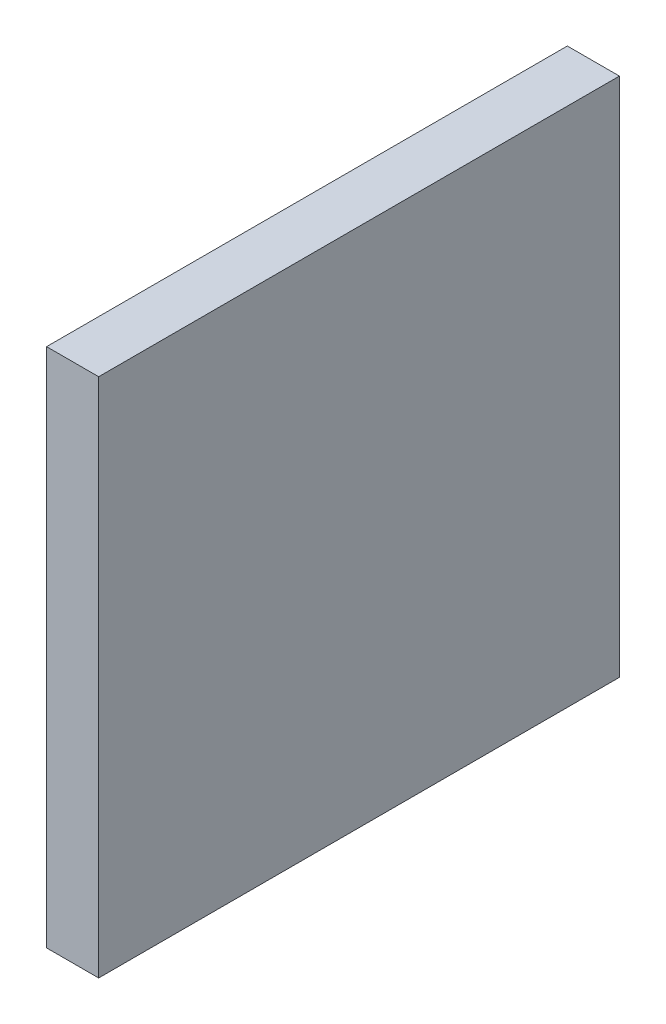
SolidWorks part; units mm, degrees
ref_plane "Front Plane" through (0, 0, 0) normal (0, 0, 1) x (1, 0, 0)
ref_plane "Top Plane" through (0, 0, 0) normal (0, 1, 0) x (1, 0, 0)
ref_plane "Right Plane" through (0, 0, 0) normal (1, 0, 0) x (0, 0, -1)
sketch "Sketch2" plane through (0, 0, 0) normal (1, 0, 0) x (0, 0, -1)
  line L1 (0, 0) -> (1000, 0)
  line L2 (0, 0) -> (0, -1000)
  line L3 (0, -1000) -> (1000, -1000)
  line L4 (1000, 0) -> (1000, -1000)
  dimension "D1" = 1000
  dimension "D2" = 1000
extrude "Boss-Extrude2" add sketch "Sketch2" along normal blind 100 contours L2 L1 L4 L3
sketch "Sketch4" plane through (0, 0, 0) normal (-1, 0, 0) x (0, 0, 1)
  line L1 (-637.0515, -497.8398) -> (-491.3115, -497.8398)
  line L2 (-637.0515, -497.8398) -> (-637.0515, -362.0998)
  line L3 (-637.0515, -362.0998) -> (-491.3115, -362.0998)
  line L4 (-491.3115, -497.8398) -> (-491.3115, -362.0998)
  dimension "D1" = 145.74
  dimension "D2" = 135.74
extrude "Boss-Extrude4" add sketch "Sketch4" along normal blind 8 contours L2 L1 L4 L3
fillet "Fillet1" radius 10 4 edges at (-4, -362.0998, -491.3115) (-4, -497.8398, -491.3115) (-4, -362.0998, -637.0515) (-4, -497.8398, -637.0515)
sketch "Sketch11" plane through (-8, 0, 0) normal (-1, 0, 0) x (0, 0, 1)
  line L2 (-611.7925, -486.8408) -> (-512.3105, -486.8408)
  line L3 (-611.7925, -486.8408) -> (-611.7925, -387.3588)
  line L4 (-611.7925, -387.3588) -> (-512.3105, -387.3588)
  line L5 (-512.3105, -486.8408) -> (-512.3105, -387.3588)
  line L6 (-611.7925, -486.8408) -> (-512.3105, -387.3588) construction
  line L7 (-611.7925, -387.3588) -> (-512.3105, -486.8408) construction
  point P4 (-562.0515, -437.0998)
extrude "Boss-Extrude6" add sketch "Sketch11" along normal blind 10 contours L3 L2 L5 L4
sketch "Sketch12" plane through (0, -486.8408, 0) normal (0, -1, 0) x (-1, 0, 0)
  line L0 (8, 611.7925) -> (18, 512.3105)
  line L1 (18, 611.7925) -> (18, 512.3105) construction
  line L2 (18, 512.3105) -> (18, 611.7925)
  line L3 (18, 611.7925) -> (8, 611.7925)
extrude "Cut-Extrude2" cut sketch "Sketch12" against normal blind 199
fillet "Fillet5" radius 5 2 edges at (-13, -387.3588, -512.3105) (-13, -486.8408, -512.3105)
sketch "Sketch13" plane through (-8, 0, 0) normal (-1, 0, 0) x (0, 0, 1)
  line L6 (-637.0515, -487.8398) -> (-637.0515, -372.0998) construction
  line L7 (-637.0515, -361.8227) -> (-491.3115, -361.8227)
  line L8 (-637.0515, -361.8227) -> (-637.0515, -372.0998)
  line L9 (-637.0515, -372.0998) -> (-491.3115, -372.0998)
  line L10 (-491.3115, -361.8227) -> (-491.3115, -372.0998)
extrude "Cut-Extrude3" cut sketch "Sketch13" against normal blind 8
fillet "Fillet6" radius 10 2 edges at (-4, -372.0998, -491.3115) (-4, -372.0998, -637.0515)
